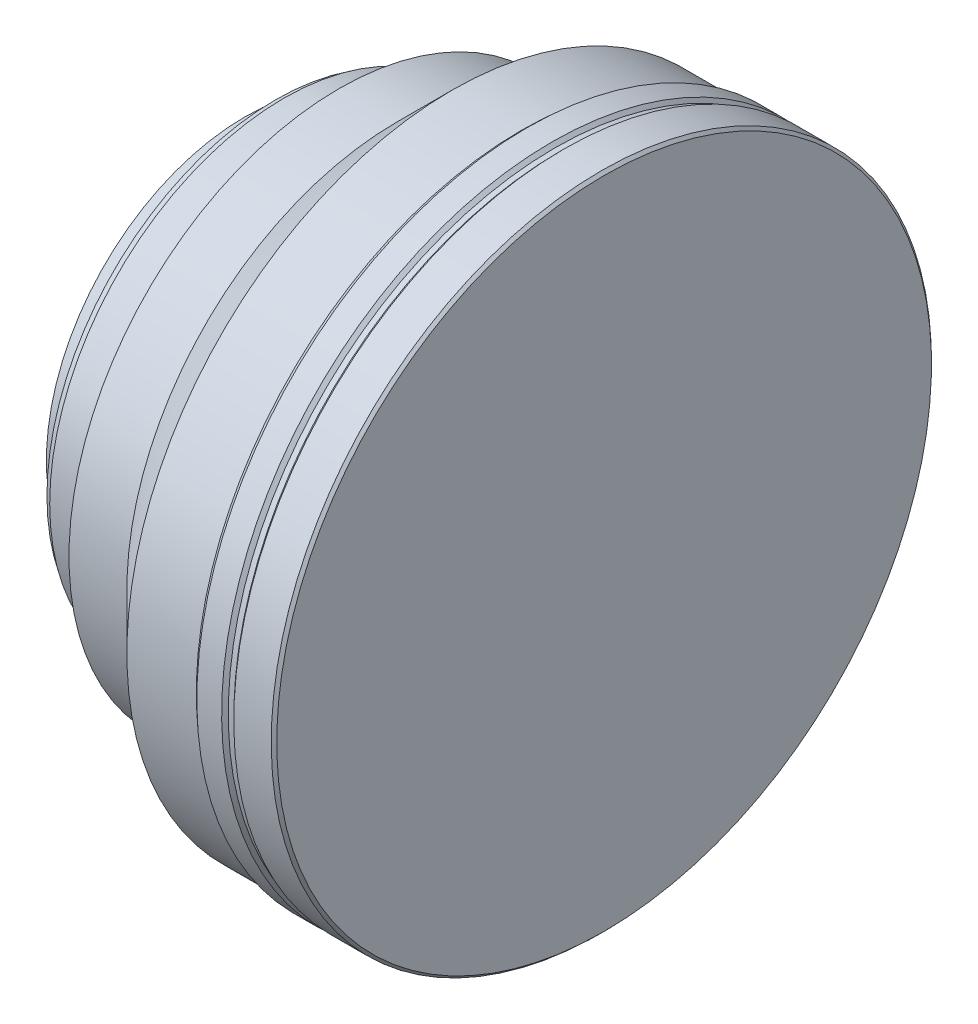
SolidWorks part; units mm, degrees
material "CA"
ref_plane "Front Plane" through (0, 0, 0) normal (0, 0, 1) x (1, 0, 0)
ref_plane "Top Plane" through (0, 0, 0) normal (0, 1, 0) x (1, 0, 0)
ref_plane "Right Plane" through (0, 0, 0) normal (1, 0, 0) x (0, 0, -1)
sketch "Sketch1" plane through (0, 0, 0) normal (0, 0, 1) x (1, 0, 0)
  line L0 (0, 0) -> (0, 59.9)
  line L1 (0, 59.9) -> (-7.3, 59.9)
  line L2 (-15, 59) -> (-14, 59.9)
  line L3 (0, 0) -> (-96.5285, 0) construction
  line L4 (-48.1, 45.25) -> (-48.8, 45.25)
  line L5 (-15, 59) -> (-27.6, 59)
  line L6 (-27.6, 59) -> (-37.6, 49)
  line L7 (-37.6, 49) -> (-48.1, 49)
  line L8 (-48.1, 49) -> (-48.1, 45.25)
  line L9 (-48.8, 45.25) -> (-48.8, 41.5)
  line L10 (-48.8, 41.5) -> (-50.8, 41.5)
  line L11 (-50.8, 41.5) -> (-50.8, 42.5)
  line L12 (-50.8, 42.5) -> (-58.1, 42.5)
  line L13 (-58.1, 42.5) -> (-58.1, 41.5)
  line L14 (-58.1, 41.5) -> (-59.6, 41.5)
  line L15 (-59.6, 41.5) -> (-59.6, 36)
  line L16 (-59.6, 36) -> (-65.2, 36)
  line L17 (-65.2, 36) -> (-65.2, 32)
  line L18 (-65.2, 32) -> (-66.2, 32)
  line L19 (-66.2, 32) -> (-66.2, 0)
  line L20 (0, 0) -> (-66.2, 0)
  line L21 (-9.5, 59.9) -> (-8.9, 59.3)
  line L22 (-8.9, 59.3) -> (-7.9, 59.3)
  line L23 (-7.9, 59.3) -> (-7.3, 59.9)
  line L24 (-8.4, 59.3) -> (-8.4, 59.9) construction
  line L25 (-9.5, 59.9) -> (-14, 59.9)
  dimension "D1" = 59.9
  dimension "D2" = 14
  dimension "D3" = 59
  dimension "D4" = 1
  dimension "D5" = 45
  dimension "D6" = 49
  dimension "D7" = 10.5
  dimension "D8" = 0.7
  dimension "D9" = 45.25
  dimension "D10" = 42.5
  dimension "D11" = 2
  dimension "D12" = 1.5
  dimension "D13" = 11.5
  dimension "D14" = 1
  dimension "D15" = 18.1
  dimension "D16" = 36
  dimension "D17" = 32
  dimension "D18" = 66.2
  dimension "D19" = 45
  dimension "D20" = 45
  dimension "D21" = 0.6
  dimension "D22" = 4.5
  dimension "D23" = 1
revolve "Revolve1" add sketch "Sketch1" angle 360 about L20
chamfer "Chamfer1" distance 0.5 angle 45 1 edges at (0, 59.9, 0)
